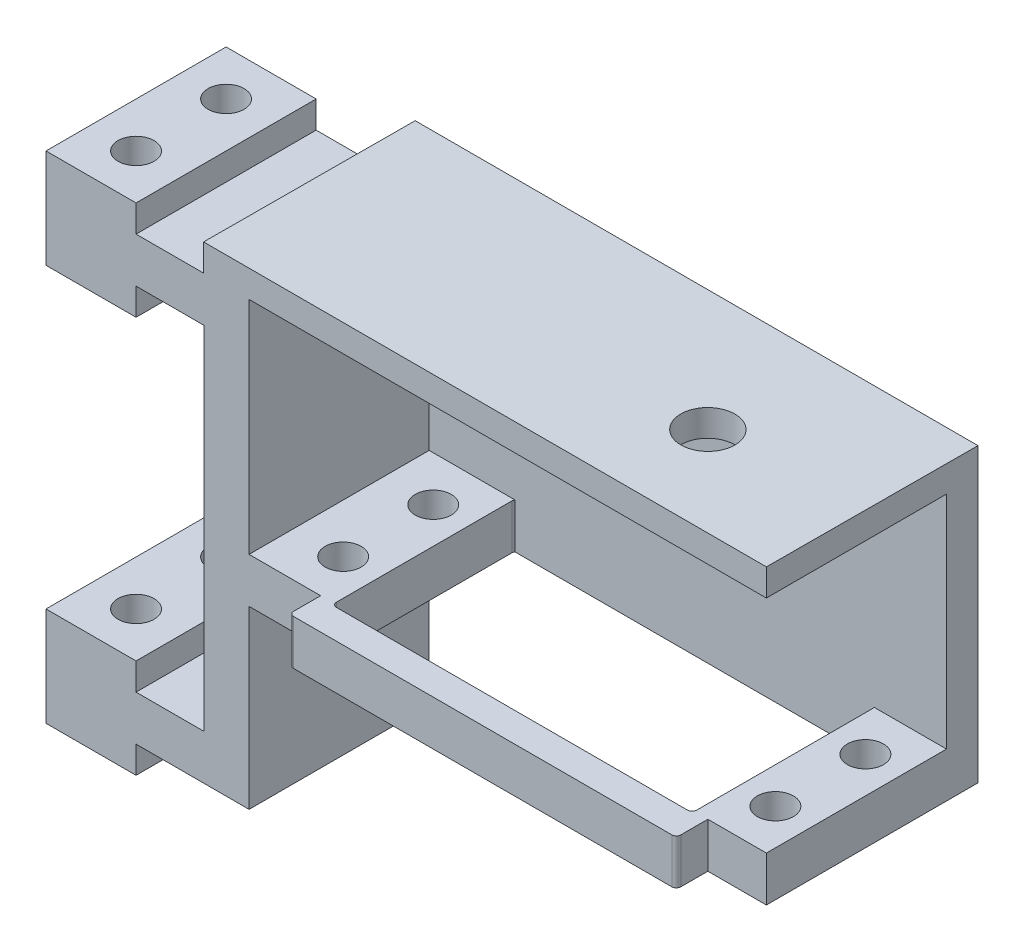
SolidWorks part; units mm, degrees
ref_plane "Front Plane" through (0, 0, 0) normal (0, 0, 1) x (1, 0, 0)
ref_plane "Top Plane" through (0, 0, 0) normal (0, 1, 0) x (1, 0, 0)
ref_plane "Right Plane" through (0, 0, 0) normal (1, 0, 0) x (0, 0, -1)
sketch "Sketch1" plane through (0, 0, 0) normal (0, 0, 1) x (1, 0, 0)
  line L0 (0, 0) -> (12.5514, 0)
  line L1 (12.5514, 0) -> (12.5514, 19.5244)
  line L2 (12.5514, 19.5244) -> (70, 19.5244)
  line L3 (0, 5) -> (7.5514, 5)
  line L4 (7.5514, 5) -> (7.5514, 24.5244)
  line L5 (12.5514, 24.5244) -> (70, 24.5244)
  line L6 (70, 24.5244) -> (70, 19.5244)
  line L7 (0, 5) -> (0, 8)
  line L8 (0, 8) -> (-10, 8)
  line L9 (-10, 8) -> (-10, -3)
  line L10 (-10, -3) -> (0, -3)
  line L11 (0, -3) -> (0, 0)
  line L12 (0, 52.0488) -> (0, 49.0488)
  line L13 (-10, 52.0488) -> (0, 52.0488)
  line L14 (-10, 41.0488) -> (-10, 52.0488)
  line L15 (0, 41.0488) -> (-10, 41.0488)
  line L16 (0, 44.0488) -> (0, 41.0488)
  line L17 (0, 44.0488) -> (7.5514, 44.0488)
  line L18 (0, 49.0488) -> (12.5514, 49.0488)
  line L19 (7.5514, 44.0488) -> (7.5514, 24.5244)
  line L20 (12.5514, 49.0488) -> (12.5514, 24.5244)
  line L22 (7.5514, 24.5244) -> (70, 24.5244) construction
  dimension "D1" = 12.5514
  dimension "D2" = 70
  dimension "D3" = 19.5244
  dimension "D5" = 10
  dimension "D6" = 3
  dimension "D4" = 5
extrude "Boss-Extrude1" add sketch "Sketch1" along normal blind 20
sketch "Sketch2" plane through (0, 19.5244, 0) normal (0, -1, 0) x (1, 0, 0)
  line L0 (70, 10) -> (14.8173, 10) construction
  line L1 (70, 20) -> (70, 0) construction
  circle A0 centre (66, 15) radius 2
  circle A1 centre (18, 15) radius 2
  circle A2 centre (18, 5) radius 2
  circle A3 centre (66, 5) radius 2
  dimension "D1" = 4
  dimension "D4" = 5
  dimension "D5" = 5
  dimension "D6" = 48
  dimension "D7" = 4
  dimension "D2" = 2
  dimension "D3" = 2
sketch "Sketch3" plane through (-10, 0, 0) normal (-1, 0, 0) x (0, 0, 1)
  line L0 (0, 8) -> (20, -3) construction
  line L1 (20, 8) -> (0, -3) construction
  line L3 (2.5, 5) -> (17.5, 5)
  line L4 (2.5, 5) -> (2.5, 0)
  line L5 (2.5, 0) -> (17.5, 0)
  line L6 (17.5, 5) -> (17.5, 0)
  line L7 (2.5, 5) -> (17.5, 0) construction
  line L8 (2.5, 0) -> (17.5, 5) construction
  point P8 (10, 2.5)
  dimension "D1" = 5
  dimension "D2" = 15
extrude "Cut-Extrude2" cut sketch "Sketch3" against normal blind 8
mirror "Mirror1" about plane through (12.5514, 24.5244, 20) normal (0, -1, 0) of "Cut-Extrude2"
sketch "Sketch4" plane through (0, 52.0488, 0) normal (0, 1, 0) x (1, 0, 0)
  line L0 (0, -10) -> (-10, -10) construction
  line L1 (0, -20) -> (0, 0) construction
  line L2 (-10, -20) -> (-10, 0) construction
  circle A0 centre (-5, -5) radius 2
  circle A1 centre (-5, -15) radius 2
  point P10 (-5, -10)
  dimension "D1" = 4
  dimension "D2" = 4
  dimension "D3" = 5
  dimension "D4" = 5
  dimension "D5" = 5
extrude "Cut-Extrude3" cut sketch "Sketch4" against normal blind 110
extrude "Cut-Extrude4" cut sketch "Sketch2" against normal blind 110
sketch "Sketch5" plane through (0, 19.5244, 0) normal (0, -1, 0) x (1, 0, 0)
  line L0 (12.5514, 10) -> (70, 10) construction
  line L1 (12.5514, 20) -> (12.5514, 0) construction
  line L2 (70, 20) -> (70, 0) construction
  line L3 (18, 15) -> (66, 15) construction
  line L4 (42, 15) -> (42, -15.2081) construction
  line L6 (20.5, 23.5) -> (63.5, 23.5)
  line L7 (20.5, 23.5) -> (20.5, -3.5)
  line L8 (20.5, -3.5) -> (63.5, -3.5)
  line L9 (63.5, 23.5) -> (63.5, -3.5)
  line L10 (20.5, 23.5) -> (63.5, -3.5) construction
  line L11 (20.5, -3.5) -> (63.5, 23.5) construction
  point P12 (42, 10)
  dimension "D1" = 27
  dimension "D2" = 43
extrude "Boss-Extrude2" add sketch "Sketch5" against normal blind 5
sketch "Sketch6" plane through (0, 19.5244, 0) normal (0, -1, 0) x (1, 0, 0)
  line L0 (42, 23.5) -> (42, -3.5) construction
  line L1 (63.5, 23.5) -> (20.5, 23.5) construction
  line L2 (20.5, -3.5) -> (63.5, -3.5) construction
  line L3 (12.5514, 10) -> (70, 10) construction
  line L4 (12.5514, 20) -> (12.5514, 0) construction
  line L5 (70, 20) -> (70, 0) construction
  line L7 (22, 20.25) -> (62, 20.25)
  line L8 (22, 20.25) -> (22, -0.25)
  line L9 (22, -0.25) -> (62, -0.25)
  line L10 (62, 20.25) -> (62, -0.25)
  line L11 (22, 20.25) -> (62, -0.25) construction
  line L12 (22, -0.25) -> (62, 20.25) construction
  point P12 (42, 10)
  dimension "D1" = 20.5
  dimension "D2" = 40
extrude "Cut-Extrude5" cut sketch "Sketch6" against normal blind 5
fillet "Fillet1" radius 0.5 8 edges at (20.5, 22.0244, -3.5) (63.5, 22.0244, -3.5) (63.5, 22.0244, 23.5) (20.5, 22.0244, 23.5) (62, 22.0244, -0.25) (22, 22.0244, -0.25) (62, 22.0244, 20.25) (22, 22.0244, 20.25)
ref_plane "Plane1" through (70, 0, 0) normal (1, 0, 0) x (0, 0, -1)
sketch "Sketch7" plane through (70, 0, 0) normal (1, 0, 0) x (0, 0, -1)
  line L0 (0, 19.5244) -> (3.5, 19.5244)
  line L1 (3.5, 19.5244) -> (3.5, 51.9588)
  line L2 (3.5, 51.9588) -> (-20, 52.0488)
  line L3 (-20, 52.0488) -> (-20, 49.0488)
  line L4 (-20, 49.0488) -> (0, 49.0488)
  line L5 (0, 49.0488) -> (0, 52.0488) construction
  line L6 (-20, 49.0488) -> (0, 49.0488) construction
  line L7 (0, 49.0488) -> (0, 19.5244)
  dimension "D1" = 32.4344
extrude "Boss-Extrude3" add sketch "Sketch7" against normal blind 62.5
sketch "Sketch8" plane through (0, 51.9715, -0.199) normal (0, 1, -0.0038) x (1, 0, 0)
  line L0 (65.2186, -10.199) -> (40.4718, -10.199) construction
  line L1 (7.5, 3.301) -> (70, 3.301) construction
  line L2 (70, -18.1151) -> (70, 18.1151) construction
  circle A0 centre (53.5, -10.199) radius 3
  dimension "D1" = 6
  dimension "D2" = 13.5
  dimension "D3" = 16.5
extrude "Cut-Extrude6" cut sketch "Sketch8" against normal blind 62.5
